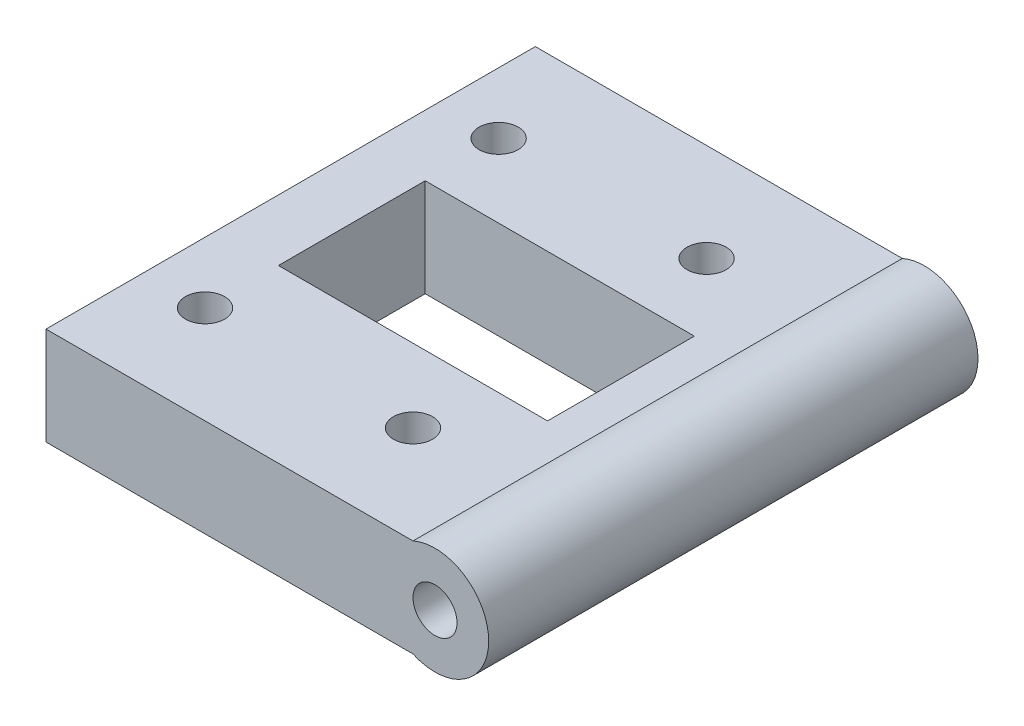
SolidWorks part; units mm, degrees
ref_plane "前视基准面" through (0, 0, 0) normal (0, 0, 1) x (1, 0, 0)
ref_plane "上视基准面" through (0, 0, 0) normal (0, 1, 0) x (1, 0, 0)
ref_plane "右视基准面" through (0, 0, 0) normal (1, 0, 0) x (0, 0, -1)
sketch "草图1" plane through (0, 0, 0) normal (0, 1, 0) x (1, 0, 0)
  line L1 (51.3695, -22.0464) -> (21.3695, -22.0464)
  line L2 (51.3695, -22.0464) -> (51.3695, 17.9536)
  line L3 (51.3695, 17.9536) -> (21.3695, 17.9536)
  line L4 (21.3695, -22.0464) -> (21.3695, 17.9536)
  point P0 (0, 0)
  dimension "D1" = 40
  dimension "D2" = 30
extrude "凸台-拉伸1" add sketch "草图1" along normal blind 8
sketch "草图2" plane through (0, 0, 22.0464) normal (0, 0, 1) x (1, 0, 0)
  line L0 (21.3695, 4) -> (64.5589, 4) construction
  line L1 (21.3695, 8) -> (21.3695, 0) construction
  line L2 (51.3695, 8) -> (51.3695, 0) construction
  circle A0 centre (53.1695, 4) radius 1.8
  circle A1 centre (53.1695, 4) radius 4.3863
  dimension "D1" = 1.8
extrude "凸台-拉伸2" add sketch "草图2" against normal blind 40
sketch "草图3" plane through (0, 8, 0) normal (0, 1, 0) x (1, 0, 0)
  line L0 (21.3695, -2.0464) -> (51.3695, -2.0464) construction
  line L1 (21.3695, 17.9536) -> (21.3695, -22.0464) construction
  line L2 (51.3695, -22.0464) -> (51.3695, 17.9536) construction
  circle A0 centre (26.3695, 9.9536) radius 1.6
  circle A1 centre (43.3695, 9.9536) radius 1.6
  circle A2 centre (43.3695, -14.0464) radius 1.6
  circle A3 centre (26.3695, -14.0464) radius 1.6
  dimension "D1" = 12
  dimension "D3" = 17
  dimension "D2" = 5
extrude "切除-拉伸1" cut sketch "草图3" against normal through all
sketch "草图4" plane through (0, 8, 0) normal (0, 1, 0) x (1, 0, 0)
  line L0 (51.3695, 17.9536) -> (21.3695, 17.9536) construction
  line L1 (48.3695, -8.0464) -> (26.3695, -8.0464)
  line L2 (48.3695, -8.0464) -> (48.3695, 3.9536)
  line L3 (48.3695, 3.9536) -> (26.3695, 3.9536)
  line L4 (26.3695, -8.0464) -> (26.3695, 3.9536)
  line L5 (48.3695, -8.0464) -> (26.3695, 3.9536) construction
  line L6 (48.3695, 3.9536) -> (26.3695, -8.0464) construction
  line L7 (21.3695, -22.0464) -> (51.3695, -22.0464) construction
  line L8 (21.3695, 17.9536) -> (21.3695, -22.0464) construction
  line L9 (51.3695, -22.0464) -> (51.3695, 17.9536) construction
  point P0 (37.3695, -2.0464)
  dimension "D1" = 14
  dimension "D2" = 14
  dimension "D3" = 5
  dimension "D4" = 3
extrude "切除-拉伸2" cut sketch "草图4" against normal through all
equation "\"7、\"=5"
